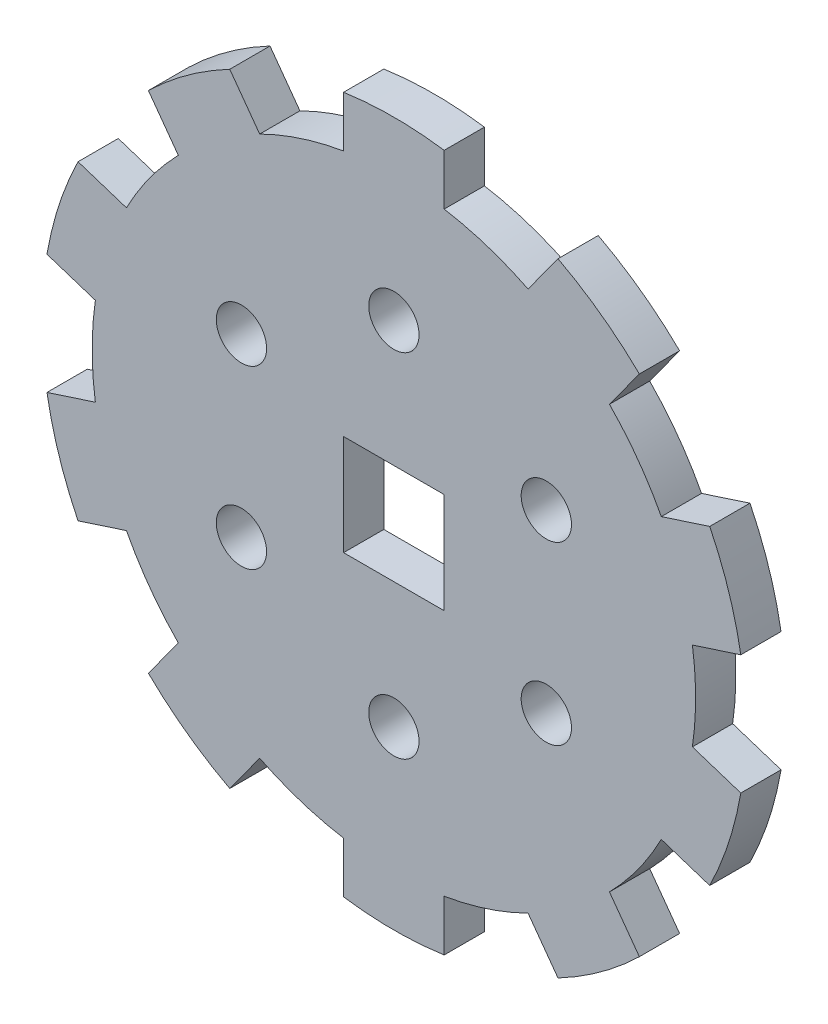
SolidWorks part; units mm, degrees
ref_plane "Front Plane" through (0, 0, 0) normal (0, 0, 1) x (1, 0, 0)
ref_plane "Top Plane" through (0, 0, 0) normal (0, 1, 0) x (1, 0, 0)
ref_plane "Right Plane" through (0, 0, 0) normal (1, 0, 0) x (0, 0, -1)
sketch "Sketch1" plane through (0, 0, 0) normal (0, 0, 1) x (1, 0, 0)
  line L0 (0, 0) -> (0, 35) construction
  line L1 (5, 29.5804) -> (5, 34.641)
  line L2 (-5, 29.5804) -> (-5, 34.641)
  line L3 (13.3418, 26.87) -> (16.3164, 30.9641)
  line L4 (21.432, 20.9921) -> (24.4066, 25.0862)
  line L5 (26.5875, 13.8961) -> (31.4005, 15.4599)
  line L6 (29.6777, 4.3856) -> (34.4906, 5.9494)
  line L7 (29.6777, -4.3856) -> (34.4906, -5.9494)
  line L8 (26.5875, -13.8961) -> (31.4005, -15.4599)
  line L9 (21.432, -20.9921) -> (24.4066, -25.0862)
  line L10 (13.3418, -26.87) -> (16.3164, -30.9641)
  line L11 (5, -29.5804) -> (5, -34.641)
  line L12 (-5, -29.5804) -> (-5, -34.641)
  line L13 (-13.3418, -26.87) -> (-16.3164, -30.9641)
  line L14 (-21.432, -20.9921) -> (-24.4066, -25.0862)
  line L15 (-26.5875, -13.8961) -> (-31.4005, -15.4599)
  line L16 (-29.6777, -4.3856) -> (-34.4906, -5.9494)
  line L17 (-29.6777, 4.3856) -> (-34.4906, 5.9494)
  line L18 (-26.5875, 13.8961) -> (-31.4005, 15.4599)
  line L19 (-21.432, 20.9921) -> (-24.4066, 25.0862)
  line L20 (-13.3418, 26.87) -> (-16.3164, 30.9641)
  line L21 (0, 0) -> (30.3109, 17.5) construction
  line L22 (-5, 5) -> (5, 5)
  line L23 (-5, 5) -> (-5, -5)
  line L24 (-5, -5) -> (5, -5)
  line L25 (5, 5) -> (5, -5)
  line L26 (-5, 5) -> (5, -5) construction
  line L27 (-5, -5) -> (5, 5) construction
  line L28 (0, 0) -> (30.3109, -17.5) construction
  line L29 (0, 0) -> (0, -35) construction
  line L30 (0, 0) -> (-30.3109, -17.5) construction
  line L31 (0, 0) -> (-30.3109, 17.5) construction
  arc A0 (-29.6777, 4.3856) -> (-29.6777, -4.3856) centre (0, 0) ccw
  arc A1 (5, 34.641) -> (-5, 34.641) centre (0, 0) ccw
  arc A2 (24.4066, 25.0862) -> (16.3164, 30.9641) centre (0, 0) ccw
  arc A3 (34.4906, 5.9494) -> (31.4005, 15.4599) centre (0, 0) ccw
  arc A4 (31.4005, -15.4599) -> (34.4906, -5.9494) centre (0, 0) ccw
  arc A5 (16.3164, -30.9641) -> (24.4066, -25.0862) centre (0, 0) ccw
  arc A6 (-5, -34.641) -> (5, -34.641) centre (0, 0) ccw
  arc A7 (-24.4066, -25.0862) -> (-16.3164, -30.9641) centre (0, 0) ccw
  arc A8 (-34.4906, -5.9494) -> (-31.4005, -15.4599) centre (0, 0) ccw
  arc A9 (-31.4005, 15.4599) -> (-34.4906, 5.9494) centre (0, 0) ccw
  arc A10 (-16.3164, 30.9641) -> (-24.4066, 25.0862) centre (0, 0) ccw
  arc A11 (-21.432, 20.9921) -> (-26.5875, 13.8961) centre (0, 0) ccw
  arc A12 (-5, 29.5804) -> (-13.3418, 26.87) centre (0, 0) ccw
  arc A13 (13.3418, 26.87) -> (5, 29.5804) centre (0, 0) ccw
  arc A14 (26.5875, 13.8961) -> (21.432, 20.9921) centre (0, 0) ccw
  arc A15 (29.6777, -4.3856) -> (29.6777, 4.3856) centre (0, 0) ccw
  arc A16 (21.432, -20.9921) -> (26.5875, -13.8961) centre (0, 0) ccw
  arc A17 (5, -29.5804) -> (13.3418, -26.87) centre (0, 0) ccw
  arc A18 (-13.3418, -26.87) -> (-5, -29.5804) centre (0, 0) ccw
  arc A19 (-26.5875, -13.8961) -> (-21.432, -20.9921) centre (0, 0) ccw
  circle A20 centre (0, 17.5) radius 2.5
  circle A21 centre (15.1554, 8.75) radius 2.5
  circle A22 centre (15.1554, -8.75) radius 2.5
  circle A23 centre (0, -17.5) radius 2.5
  circle A24 centre (-15.1554, -8.75) radius 2.5
  circle A25 centre (-15.1554, 8.75) radius 2.5
  point P47 (0, 0)
  point P64 (0, 0)
  point P69 (0, 0)
  dimension "D1" = 60
  dimension "D4" = 10
  dimension "D2" = 70
  dimension "D7" = 5
  dimension "D3" = 5
  dimension "D6" = 10
  dimension "D9" = 6
  dimension "D5" = 10
  dimension "D8" = 6
extrude "Boss-Extrude1" add sketch "Sketch1" along normal blind 4
